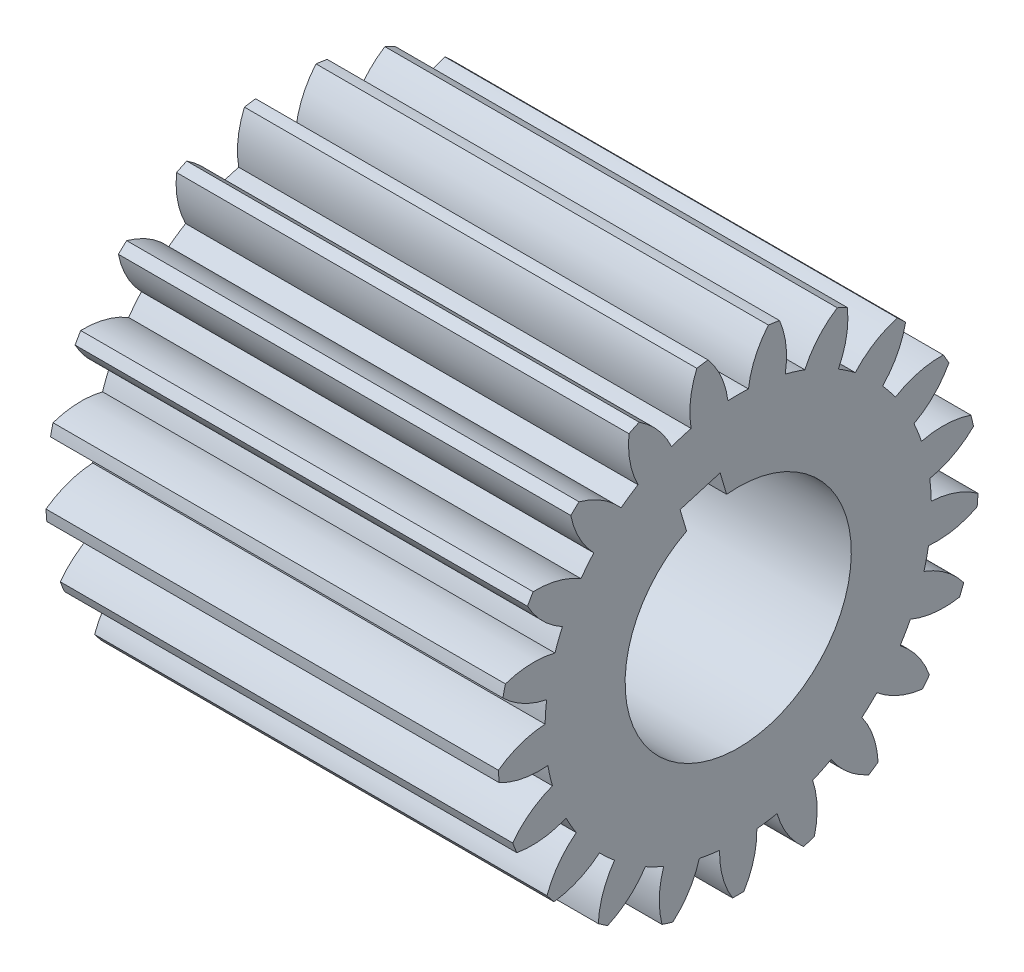
SolidWorks part; units mm, degrees
ref_plane "Plane1" through (0, 0, 0) normal (0, 0, 1) x (1, 0, 0)
ref_plane "Plane2" through (0, 0, 0) normal (0, 1, 0) x (1, 0, 0)
ref_plane "Plane3" through (0, 0, 0) normal (1, 0, 0) x (0, 0, -1)
other "Configuration Table"
sketch "HoldingSke" plane through (0, 0, 0) normal (0, 1, 0) x (1, 0, 0)
  line L0 (0, 0) -> (0.1556, -0.0597)
  line L1 (-15, 0) -> (100, 0) construction
  line L2 (0, 0) -> (-2.1039, 2.3779)
  line L3 (0, 0) -> (-11.863, 4.5341)
  line L4 (0, 0) -> (8.0624, 3.0949)
  line L5 (0, 0) -> (-46.8476, -17.4728)
  line L6 (0, 0) -> (-107.7652, -72.7095)
  line L7 (-2.1039, 2.3779) -> (25.8785, 129.3306)
  line L8 (-76.2, 54.61) -> (-71.3, 54.61)
  line L9 (-71.009, 38.7566) -> (-53.1078, 45.2721)
  line L10 (-76.2, 71.12) -> (104.1128, 71.12)
  line L11 (0, 0) -> (-130, 0)
  line L12 (-76.2, 101.6) -> (-75.993, 101.6)
  line L13 (24.9733, 27.94) -> (52.9518, 28.4284)
  line L14 (24.9733, 27.94) -> (24.9743, 27.94)
  line L15 (24.9733, 27.94) -> (100.4006, 29.5858)
  line L16 (-63.627, -6) -> (-12.827, -6)
  circle A0 centre (0, 0) radius 32.5
  circle A1 centre (0, 0) radius 37.5
  circle A2 centre (0, 0) radius 37.5
  circle A3 centre (0, 0) radius 32.5
  dimension "MHD" = 75
  dimension "Hub_dia" = 75
  dimension "Bore" = 65
  dimension "MBD" = 65
  dimension "Num_teeth" = 21
  dimension "Pitch" = 0.1667
  dimension "Overall_len" = 50
  dimension "Show_teeth" = 21
  dimension "Thickness" = 130
  dimension "OAL" = 130.0001
  dimension "T_dim" = 4.9
  dimension "Ap" = 20
  dimension "H" = 19.05
  dimension "Pitch_radius" = 180.3128
  dimension "Width" = 130
  dimension "Backlash" = 0.207
  dimension "Addendum_fac" = 1
  dimension "Dedendum_fac" = 1.25
  dimension "Clearance_fac" = 0.25
  dimension "Dedendum_add" = 0.001
  dimension "Module" = 6
sketch "BasProSke" plane through (0, 0, 0) normal (0, 1, 0) x (1, 0, 0)
  line L0 (-10, 0) -> (60, 0) construction
  line L1 (0, 0) -> (0, 69)
  line L2 (0, 0) -> (130, 0)
  line L3 (130, 0) -> (130, 69)
  line L4 (130, 69) -> (0, 69)
  dimension "Thickness" = 130
  dimension "Diameter" = 138
revolve "Base-Revolve" add sketch "BasProSke" angle 360 about L0
sketch "TooCutSke" plane through (0, 0, 0) normal (1, 0, 0) x (0, 0, -1)
  line L1 (0, 0) -> (0, 107) construction
  line L2 (0, 0) -> (-5.0701, 62.7957) construction
  line L3 (0, 0) -> (-18.7346, 124.2959) construction
  line L4 (-5.0701, 62.7957) -> (-9.3673, 62.148) construction
  arc A0 (2.9399, 55.4211) -> (-2.9399, 55.4211) centre (0, 0) ccw
  arc A1 (8.6963, 68.4754) -> (-8.6963, 68.4754) centre (0, 0) ccw
  circle A2 centre (0, 0) radius 63 construction
  circle A3 centre (0, 0) radius 59.2006 construction
  arc A4 (-2.9399, 55.4211) -> (-8.6963, 68.4754) centre (-27.9327, 52.1965) ccw
  arc A5 (8.6963, 68.4754) -> (2.9399, 55.4211) centre (27.9327, 52.1965) ccw
  dimension "Root_dia" = 110.998
  dimension "Overcut_dia" = 138.0508
  dimension "Pitch_dia" = 126
  dimension "Base_dia" = 118.4013
  dimension "Flank_rad" = 25.2
  dimension "Half_ang" = 8.571
  dimension "Half_CT" = 4.3457
extrude "ToothCut" cut sketch "TooCutSke" along normal through all
fillet "Breaks" [suppressed] radius 0.12
fillet "RootFillets" [suppressed] radius 1.501
pattern_circular "TeethCuts" count 21 every 17.143 about axis through (-10, 0, 0) along (1, 0, 0) of "ToothCut", "RootFillets", "Breaks"
sketch "HubNeaOneSke" plane through (0, 0, 0) normal (-1, 0, 0) x (0, 0, 1)
  circle A0 centre (0, 0) radius 37.5
  dimension "Diameter" = 75
extrude "HubNearOne" [suppressed] add sketch "HubNeaOneSke" along normal blind 38.0001
sketch "HubNeaBotSke" plane through (0, 0, 0) normal (-1, 0, 0) x (0, 0, 1)
  circle A0 centre (0, 0) radius 37.5
  dimension "Diameter" = 75
extrude "HubNearBoth" [suppressed] add sketch "HubNeaBotSke" along normal blind 19
ref_plane "FarPln" through (130, 0, 0) normal (1, 0, 0) x (0, 0, -1)
sketch "HubFarSke" plane through (130, 0, 0) normal (1, 0, 0) x (0, 0, -1)
  circle A0 centre (0, 0) radius 37.5
  dimension "Diameter" = 75
extrude "HubFar" [suppressed] add sketch "HubFarSke" along normal blind 19
sketch "BorSke" plane through (0, 0, 0) normal (1, 0, 0) x (0, 0, -1)
  circle A0 centre (0, 0) radius 32.5
  dimension "Diameter" = 65
extrude "Bore" cut sketch "BorSke" along normal mid plane 260.0001
sketch "KeySke" plane through (0, 0, 0) normal (1, 0, 0) x (0, 0, -1)
  line L0 (-10, 0) -> (-10, 37.4)
  line L1 (-10, 37.4) -> (10, 37.4)
  line L2 (10, 37.4) -> (10, 0)
  line L3 (0, 0) -> (0, 34) construction
  line L4 (-10, 0) -> (10, 0)
  dimension "Offset" = 37.4
  dimension "Width" = 20
extrude "Keyway" [suppressed] cut sketch "KeySke" along normal mid plane 260.0001
pattern_circular "Keyway2" [suppressed] count 2 every 90 about axis through (-10, 0, 0) along (1, 0, 0)
sketch "Sketch1" plane through (0, 0, 0) normal (-1, 0, 0) x (0, 0, 1)
  line L0 (16.6951, 35.2069) -> (5.19, 38.6175) construction
  line L1 (16.6951, 35.2069) -> (5.19, 38.6175)
  line L2 (5.19, 38.6175) -> (1.7794, 27.1124) construction
  line L3 (13.2845, 23.7018) -> (1.7794, 27.1124) construction
  line L4 (16.6951, 35.2069) -> (13.2845, 23.7018) construction
  line L5 (5.19, 38.6175) -> (1.7794, 27.1124)
  line L6 (13.2845, 23.7018) -> (1.7794, 27.1124)
  line L7 (16.6951, 35.2069) -> (13.2845, 23.7018)
  arc A84 (55.0464, 7.0733) -> (67.6125, 13.7679) centre (49.9632, 31.7552) ccw
  arc A85 (67.6125, 13.7679) -> (66.8904, 16.9315) centre (0, 0) ccw
  arc A86 (66.8904, 16.9315) -> (52.6641, 17.511) centre (58.7934, -6.9323) ccw
  arc A87 (52.6641, 17.511) -> (50.516, 22.9842) centre (0, 0) ccw
  arc A88 (50.516, 22.9842) -> (60.5505, 33.0854) centre (38.3834, 45.0714) ccw
  arc A89 (60.5505, 33.0854) -> (58.928, 35.8955) centre (0, 0) ccw
  arc A90 (58.928, 35.8955) -> (45.1629, 32.256) centre (58.2247, 10.7054) ccw
  arc A91 (45.1629, 32.256) -> (41.497, 36.8529) centre (0, 0) ccw
  arc A92 (41.497, 36.8529) -> (48.1083, 49.4631) centre (23.3932, 54.3827) ccw
  arc A93 (48.1083, 49.4631) -> (45.7296, 51.6701) centre (0, 0) ccw
  arc A94 (45.7296, 51.6701) -> (33.6488, 44.135) centre (52.4824, 27.3918) ccw
  arc A95 (33.6488, 44.135) -> (28.7908, 47.4471) centre (0, 0) ccw
  arc A96 (28.7908, 47.4471) -> (31.3915, 61.4457) centre (6.3243, 58.8619) ccw
  arc A97 (31.3915, 61.4457) -> (28.4679, 62.8536) centre (0, 0) ccw
  arc A98 (28.4679, 62.8536) -> (19.1449, 52.0923) centre (42.0769, 41.6443) ccw
  arc A99 (19.1449, 52.0923) -> (13.5264, 53.8254) centre (0, 0) ccw
  arc A100 (13.5264, 53.8254) -> (11.8854, 67.9687) centre (-11.3065, 58.1109) ccw
  arc A101 (11.8854, 67.9687) -> (8.6768, 68.4523) centre (0, 0) ccw
  arc A102 (8.6768, 68.4523) -> (2.9399, 55.4211) centre (27.9327, 52.1965) ccw
  arc A103 (2.9399, 55.4211) -> (-2.9399, 55.4211) centre (0, 0) ccw
  arc A104 (-2.9399, 55.4211) -> (-8.6768, 68.4523) centre (-27.9327, 52.1965) ccw
  arc A105 (-8.6768, 68.4523) -> (-11.8854, 67.9687) centre (0, 0) ccw
  arc A106 (-11.8854, 67.9687) -> (-13.5264, 53.8254) centre (11.3065, 58.1109) ccw
  arc A107 (-13.5264, 53.8254) -> (-19.1449, 52.0923) centre (0, 0) ccw
  arc A108 (-19.1449, 52.0923) -> (-28.4679, 62.8536) centre (-42.0769, 41.6443) ccw
  arc A109 (-28.4679, 62.8536) -> (-31.3915, 61.4457) centre (0, 0) ccw
  arc A110 (-31.3915, 61.4457) -> (-28.7908, 47.4471) centre (-6.3243, 58.8619) ccw
  arc A111 (-28.7908, 47.4471) -> (-33.6488, 44.135) centre (0, 0) ccw
  arc A112 (-33.6488, 44.135) -> (-45.7296, 51.6701) centre (-52.4824, 27.3918) ccw
  arc A113 (-45.7296, 51.6701) -> (-48.1083, 49.4631) centre (0, 0) ccw
  arc A114 (-48.1083, 49.4631) -> (-41.497, 36.8529) centre (-23.3932, 54.3827) ccw
  arc A115 (-41.497, 36.8529) -> (-45.1629, 32.256) centre (0, 0) ccw
  arc A116 (-45.1629, 32.256) -> (-58.928, 35.8955) centre (-58.2247, 10.7054) ccw
  arc A117 (-58.928, 35.8955) -> (-60.5505, 33.0854) centre (0, 0) ccw
  arc A118 (-60.5505, 33.0854) -> (-50.516, 22.9842) centre (-38.3834, 45.0714) ccw
  arc A119 (-50.516, 22.9842) -> (-52.6641, 17.511) centre (0, 0) ccw
  arc A120 (-52.6641, 17.511) -> (-66.8904, 16.9315) centre (-58.7934, -6.9323) ccw
  arc A121 (-66.8904, 16.9315) -> (-67.6125, 13.7679) centre (0, 0) ccw
  arc A122 (-67.6125, 13.7679) -> (-55.0464, 7.0733) centre (-49.9632, 31.7552) ccw
  arc A123 (-55.0464, 7.0733) -> (-55.4858, 1.21) centre (0, 0) ccw
  arc A124 (-55.4858, 1.21) -> (-68.9093, -3.537) centre (-54.138, -23.9539) ccw
  arc A125 (-68.9093, -3.537) -> (-68.6668, -6.7729) centre (0, 0) ccw
  arc A126 (-68.6668, -6.7729) -> (-54.6857, -9.4662) centre (-57.1035, 15.6175) ccw
  arc A127 (-54.6857, -9.4662) -> (-53.3774, -15.1985) centre (0, 0) ccw
  arc A128 (-53.3774, -15.1985) -> (-64.8053, -23.6913) centre (-44.6723, -38.8472) ccw
  arc A129 (-64.8053, -23.6913) -> (-63.6198, -26.7118) centre (0, 0) ccw
  arc A130 (-63.6198, -26.7118) -> (-49.466, -25.1646) centre (-59.1699, -1.9078) ccw
  arc A131 (-49.466, -25.1646) -> (-46.5261, -30.2565) centre (0, 0) ccw
  arc A132 (-46.5261, -30.2565) -> (-54.943, -41.7404) centre (-31.2372, -50.2887) ccw
  arc A133 (-54.943, -41.7404) -> (-52.9199, -44.2774) centre (0, 0) ccw
  arc A134 (-52.9199, -44.2774) -> (-39.851, -38.6269) centre (-55.9788, -19.2637) ccw
  arc A135 (-39.851, -38.6269) -> (-35.5408, -42.6261) centre (0, 0) ccw
  arc A136 (-35.5408, -42.6261) -> (-40.1989, -56.0808) centre (-15.0266, -57.2618) ccw
  arc A137 (-40.1989, -56.0808) -> (-37.5178, -57.9087) centre (0, 0) ccw
  arc A138 (-37.5178, -57.9087) -> (-26.695, -48.6571) centre (-47.8137, -34.9079) ccw
  arc A139 (-26.695, -48.6571) -> (-21.3976, -51.2082) centre (0, 0) ccw
  arc A140 (-21.3976, -51.2082) -> (-21.8828, -65.4381) centre (2.5193, -59.147) ccw
  arc A141 (-21.8828, -65.4381) -> (-18.7821, -66.3945) centre (0, 0) ccw
  arc A142 (-18.7821, -66.3945) -> (-11.1671, -54.3639) centre (-35.4002, -47.4504) ccw
  arc A143 (-11.1671, -54.3639) -> (-5.3531, -55.2402) centre (0, 0) ccw
  arc A144 (-5.3531, -55.2402) -> (-1.6224, -68.9809) centre (19.8412, -55.7767) ccw
  arc A145 (-1.6224, -68.9809) -> (1.6224, -68.9809) centre (0, 0) ccw
  arc A146 (1.6224, -68.9809) -> (5.3531, -55.2402) centre (-19.8412, -55.7767) ccw
  arc A147 (5.3531, -55.2402) -> (11.1671, -54.3639) centre (0, 0) ccw
  arc A148 (11.1671, -54.3639) -> (18.7821, -66.3945) centre (35.4002, -47.4504) ccw
  arc A149 (18.7821, -66.3945) -> (21.8828, -65.4381) centre (0, 0) ccw
  arc A150 (21.8828, -65.4381) -> (21.3976, -51.2082) centre (-2.5193, -59.147) ccw
  arc A151 (21.3976, -51.2082) -> (26.695, -48.6571) centre (0, 0) ccw
  arc A152 (26.695, -48.6571) -> (37.5178, -57.9087) centre (47.8137, -34.9079) ccw
  arc A153 (37.5178, -57.9087) -> (40.1989, -56.0808) centre (0, 0) ccw
  arc A154 (40.1989, -56.0808) -> (35.5408, -42.6261) centre (15.0266, -57.2618) ccw
  arc A155 (35.5408, -42.6261) -> (39.851, -38.6269) centre (0, 0) ccw
  arc A156 (39.851, -38.6269) -> (52.9199, -44.2774) centre (55.9788, -19.2637) ccw
  arc A157 (52.9199, -44.2774) -> (54.943, -41.7404) centre (0, 0) ccw
  arc A158 (54.943, -41.7404) -> (46.5261, -30.2565) centre (31.2372, -50.2887) ccw
  arc A159 (46.5261, -30.2565) -> (49.466, -25.1646) centre (0, 0) ccw
  arc A160 (49.466, -25.1646) -> (63.6198, -26.7118) centre (59.1699, -1.9078) ccw
  arc A161 (63.6198, -26.7118) -> (64.8053, -23.6913) centre (0, 0) ccw
  arc A162 (64.8053, -23.6913) -> (53.3774, -15.1985) centre (44.6723, -38.8472) ccw
  arc A163 (53.3774, -15.1985) -> (54.6857, -9.4662) centre (0, 0) ccw
  arc A164 (54.6857, -9.4662) -> (68.6668, -6.7729) centre (57.1035, 15.6175) ccw
  arc A165 (68.6668, -6.7729) -> (68.9093, -3.537) centre (0, 0) ccw
  arc A166 (68.9093, -3.537) -> (55.4858, 1.21) centre (54.138, -23.9539) ccw
  arc A167 (55.4858, 1.21) -> (55.0464, 7.0733) centre (0, 0) ccw
  arc A168 (55.0464, 7.0733) -> (67.6125, 13.7679) centre (49.9632, 31.7552) ccw
  arc A169 (67.6125, 13.7679) -> (66.8904, 16.9315) centre (0, 0) ccw
  arc A170 (66.8904, 16.9315) -> (52.6641, 17.511) centre (58.7934, -6.9323) ccw
  arc A171 (52.6641, 17.511) -> (50.516, 22.9842) centre (0, 0) ccw
  arc A172 (50.516, 22.9842) -> (60.5505, 33.0854) centre (38.3834, 45.0714) ccw
  arc A173 (60.5505, 33.0854) -> (58.928, 35.8955) centre (0, 0) ccw
  arc A174 (58.928, 35.8955) -> (45.1629, 32.256) centre (58.2247, 10.7054) ccw
  arc A175 (45.1629, 32.256) -> (41.497, 36.8529) centre (0, 0) ccw
  arc A176 (41.497, 36.8529) -> (48.1083, 49.4631) centre (23.3932, 54.3827) ccw
  arc A177 (48.1083, 49.4631) -> (45.7296, 51.6701) centre (0, 0) ccw
  arc A178 (45.7296, 51.6701) -> (33.6488, 44.135) centre (52.4824, 27.3918) ccw
  arc A179 (33.6488, 44.135) -> (28.7908, 47.4471) centre (0, 0) ccw
  arc A180 (28.7908, 47.4471) -> (31.3915, 61.4457) centre (6.3243, 58.8619) ccw
  arc A181 (31.3915, 61.4457) -> (28.4679, 62.8536) centre (0, 0) ccw
  arc A182 (28.4679, 62.8536) -> (19.1449, 52.0923) centre (42.0769, 41.6443) ccw
  arc A183 (19.1449, 52.0923) -> (13.5264, 53.8254) centre (0, 0) ccw
  arc A184 (13.5264, 53.8254) -> (11.8854, 67.9687) centre (-11.3065, 58.1109) ccw
  arc A185 (11.8854, 67.9687) -> (8.6768, 68.4523) centre (0, 0) ccw
  arc A186 (8.6768, 68.4523) -> (2.9399, 55.4211) centre (27.9327, 52.1965) ccw
  arc A187 (2.9399, 55.4211) -> (-2.9399, 55.4211) centre (0, 0) ccw
  arc A188 (-2.9399, 55.4211) -> (-8.6768, 68.4523) centre (-27.9327, 52.1965) ccw
  arc A189 (-8.6768, 68.4523) -> (-11.8854, 67.9687) centre (0, 0) ccw
  arc A190 (-11.8854, 67.9687) -> (-13.5264, 53.8254) centre (11.3065, 58.1109) ccw
  arc A191 (-13.5264, 53.8254) -> (-19.1449, 52.0923) centre (0, 0) ccw
  arc A192 (-19.1449, 52.0923) -> (-28.4679, 62.8536) centre (-42.0769, 41.6443) ccw
  arc A193 (-28.4679, 62.8536) -> (-31.3915, 61.4457) centre (0, 0) ccw
  arc A194 (-31.3915, 61.4457) -> (-28.7908, 47.4471) centre (-6.3243, 58.8619) ccw
  arc A195 (-28.7908, 47.4471) -> (-33.6488, 44.135) centre (0, 0) ccw
  arc A196 (-33.6488, 44.135) -> (-45.7296, 51.6701) centre (-52.4824, 27.3918) ccw
  arc A197 (-45.7296, 51.6701) -> (-48.1083, 49.4631) centre (0, 0) ccw
  arc A198 (-48.1083, 49.4631) -> (-41.497, 36.8529) centre (-23.3932, 54.3827) ccw
  arc A199 (-41.497, 36.8529) -> (-45.1629, 32.256) centre (0, 0) ccw
  arc A200 (-45.1629, 32.256) -> (-58.928, 35.8955) centre (-58.2247, 10.7054) ccw
  arc A201 (-58.928, 35.8955) -> (-60.5505, 33.0854) centre (0, 0) ccw
  arc A202 (-60.5505, 33.0854) -> (-50.516, 22.9842) centre (-38.3834, 45.0714) ccw
  arc A203 (-50.516, 22.9842) -> (-52.6641, 17.511) centre (0, 0) ccw
  arc A204 (-52.6641, 17.511) -> (-66.8904, 16.9315) centre (-58.7934, -6.9323) ccw
  arc A205 (-66.8904, 16.9315) -> (-67.6125, 13.7679) centre (0, 0) ccw
  arc A206 (-67.6125, 13.7679) -> (-55.0464, 7.0733) centre (-49.9632, 31.7552) ccw
  arc A207 (-55.0464, 7.0733) -> (-55.4858, 1.21) centre (0, 0) ccw
  arc A208 (-55.4858, 1.21) -> (-68.9093, -3.537) centre (-54.138, -23.9539) ccw
  arc A209 (-68.9093, -3.537) -> (-68.6668, -6.7729) centre (0, 0) ccw
  arc A210 (-68.6668, -6.7729) -> (-54.6857, -9.4662) centre (-57.1035, 15.6175) ccw
  arc A211 (-54.6857, -9.4662) -> (-53.3774, -15.1985) centre (0, 0) ccw
  arc A212 (-53.3774, -15.1985) -> (-64.8053, -23.6913) centre (-44.6723, -38.8472) ccw
  arc A213 (-64.8053, -23.6913) -> (-63.6198, -26.7118) centre (0, 0) ccw
  arc A214 (-63.6198, -26.7118) -> (-49.466, -25.1646) centre (-59.1699, -1.9078) ccw
  arc A215 (-49.466, -25.1646) -> (-46.5261, -30.2565) centre (0, 0) ccw
  arc A216 (-46.5261, -30.2565) -> (-54.943, -41.7404) centre (-31.2372, -50.2887) ccw
  arc A217 (-54.943, -41.7404) -> (-52.9199, -44.2774) centre (0, 0) ccw
  arc A218 (-52.9199, -44.2774) -> (-39.851, -38.6269) centre (-55.9788, -19.2637) ccw
  arc A219 (-39.851, -38.6269) -> (-35.5408, -42.6261) centre (0, 0) ccw
  arc A220 (-35.5408, -42.6261) -> (-40.1989, -56.0808) centre (-15.0266, -57.2618) ccw
  arc A221 (-40.1989, -56.0808) -> (-37.5178, -57.9087) centre (0, 0) ccw
  arc A222 (-37.5178, -57.9087) -> (-26.695, -48.6571) centre (-47.8137, -34.9079) ccw
  arc A223 (-26.695, -48.6571) -> (-21.3976, -51.2082) centre (0, 0) ccw
  arc A224 (-21.3976, -51.2082) -> (-21.8828, -65.4381) centre (2.5193, -59.147) ccw
  arc A225 (-21.8828, -65.4381) -> (-18.7821, -66.3945) centre (0, 0) ccw
  arc A226 (-18.7821, -66.3945) -> (-11.1671, -54.3639) centre (-35.4002, -47.4504) ccw
  arc A227 (-11.1671, -54.3639) -> (-5.3531, -55.2402) centre (0, 0) ccw
  arc A228 (-5.3531, -55.2402) -> (-1.6224, -68.9809) centre (19.8412, -55.7767) ccw
  arc A229 (-1.6224, -68.9809) -> (1.6224, -68.9809) centre (0, 0) ccw
  arc A230 (1.6224, -68.9809) -> (5.3531, -55.2402) centre (-19.8412, -55.7767) ccw
  arc A231 (5.3531, -55.2402) -> (11.1671, -54.3639) centre (0, 0) ccw
  arc A232 (11.1671, -54.3639) -> (18.7821, -66.3945) centre (35.4002, -47.4504) ccw
  arc A233 (18.7821, -66.3945) -> (21.8828, -65.4381) centre (0, 0) ccw
  arc A234 (21.8828, -65.4381) -> (21.3976, -51.2082) centre (-2.5193, -59.147) ccw
  arc A235 (21.3976, -51.2082) -> (26.695, -48.6571) centre (0, 0) ccw
  arc A236 (26.695, -48.6571) -> (37.5178, -57.9087) centre (47.8137, -34.9079) ccw
  arc A237 (37.5178, -57.9087) -> (40.1989, -56.0808) centre (0, 0) ccw
  arc A238 (40.1989, -56.0808) -> (35.5408, -42.6261) centre (15.0266, -57.2618) ccw
  arc A239 (35.5408, -42.6261) -> (39.851, -38.6269) centre (0, 0) ccw
  arc A240 (39.851, -38.6269) -> (52.9199, -44.2774) centre (55.9788, -19.2637) ccw
  arc A241 (52.9199, -44.2774) -> (54.943, -41.7404) centre (0, 0) ccw
  arc A242 (54.943, -41.7404) -> (46.5261, -30.2565) centre (31.2372, -50.2887) ccw
  arc A243 (46.5261, -30.2565) -> (49.466, -25.1646) centre (0, 0) ccw
  arc A244 (49.466, -25.1646) -> (63.6198, -26.7118) centre (59.1699, -1.9078) ccw
  arc A245 (63.6198, -26.7118) -> (64.8053, -23.6913) centre (0, 0) ccw
  arc A246 (64.8053, -23.6913) -> (53.3774, -15.1985) centre (44.6723, -38.8472) ccw
  arc A247 (53.3774, -15.1985) -> (54.6857, -9.4662) centre (0, 0) ccw
  arc A248 (54.6857, -9.4662) -> (68.6668, -6.7729) centre (57.1035, 15.6175) ccw
  arc A249 (68.6668, -6.7729) -> (68.9093, -3.537) centre (0, 0) ccw
  arc A250 (68.9093, -3.537) -> (55.4858, 1.21) centre (54.138, -23.9539) ccw
  arc A251 (55.4858, 1.21) -> (55.0464, 7.0733) centre (0, 0) ccw
  dimension "D1" = 0
extrude "Cut-Extrude1" cut sketch "Sketch1" against normal through all contours L7 L1 L5 L6
equation "' \"Module@HoldingSke\" = 6.35"
equation "' \"Num_teeth@HoldingSke\" = 12"
equation "' \"Ap@HoldingSke\" =  20"
equation "' \"Ap@HoldingSke\" = 20"
equation "' \"Width@HoldingSke\" = 0.5 * 25.4"
equation "' \"Hub_dia@HoldingSke\"= 1 * 25.4"
equation "' \"Hub_dia@HoldingSke\" = 1 * 25.4"
equation "' \"Overall_len@HoldingSke\" = 1.0 * 25.4"
equation "' \"Bore@HoldingSke\" = 0.75 * 25.4"
equation "' \"T_dim@HoldingSke\" = 0.1 * 25.4"
equation "' \"Width@KeySke\" = 0.25 * 25.4"
equation "' \"Show_teeth@HoldingSke\" = 13"
equation "' \"Backlash@HoldingSke\" = 0.009 * 25.4"
equation "' \"Addendum_fac@HoldingSke\" = 1.0"
equation "' \"Dedendum_fac@HoldingSke\" = 1.25"
equation "' \"Dedendum_add@HoldingSke\" = 0.00005 * 25.4"
equation "' \"Clearance_fac@HoldingSke\" = 0.25"
equation "\"Pitch@HoldingSke\" = 1 / \"Module@HoldingSke\""
equation "\"Overcut_dia@TooCutSke\" = (\"Num_teeth@HoldingSke\" + 2 * \"Addendum_fac@HoldingSke\") / \"Pitch@HoldingSke\" + 0.002 * 25.4"
equation "\"Pitch_dia@TooCutSke\" = \"Num_teeth@HoldingSke\" / \"Pitch@HoldingSke\""
equation "\"Base_dia@TooCutSke\" = \"Num_teeth@HoldingSke\" / \"Pitch@HoldingSke\" * cos((\"Ap@HoldingSke\"  * 3.14159265 / 180))"
equation "\"Root_dia@TooCutSke\" = (\"Num_teeth@HoldingSke\" + 2) / \"Pitch@HoldingSke\" - 2 * (\"Addendum_fac@HoldingSke\" + \"Dedendum_fac@HoldingSke\") / \"Pitch@HoldingSke\" - \"Dedendum_add@HoldingSke\" * 2"
equation "\"Half_ang@TooCutSke\" = 180 / \"Num_teeth@HoldingSke\""
equation "\"Half_CT@TooCutSke\" = \"Num_teeth@HoldingSke\" / \"Pitch@HoldingSke\" * sin((3.14159265 / 2 / \"Num_teeth@HoldingSke\")) / 2 - 7 * \"Backlash@HoldingSke\" / 4"
equation "\"Flank_rad@TooCutSke\" = \"Num_teeth@HoldingSke\" / \"Pitch@HoldingSke\" / 5"
equation "\"Radius@RootFillets\" = \"Clearance_fac@HoldingSke\" / \"Pitch@HoldingSke\" + \"Dedendum_add@HoldingSke\""
equation "\"Break_rad@Breaks\" = 0.02 / \"Pitch@HoldingSke\""
equation "\"Thickness@HoldingSke\" = \"Width@HoldingSke\""
equation "\"OAL@HoldingSke\" = \"Thickness@HoldingSke\""
equation "\"MHD@HoldingSke\" = (\"Num_teeth@HoldingSke\" + 2) / \"Pitch@HoldingSke\" - 2 * (\"Addendum_fac@HoldingSke\" + \"Dedendum_fac@HoldingSke\")  / \"Pitch@HoldingSke\" - \"Dedendum_add@HoldingSke\" * 2"
equation "\"MBD@HoldingSke\" = (\"Num_teeth@HoldingSke\" + 2) / \"Pitch@HoldingSke\" - 2 * (\"Addendum_fac@HoldingSke\" + \"Dedendum_fac@HoldingSke\")  / \"Pitch@HoldingSke\" - \"Dedendum_add@HoldingSke\" * 2 - 0.002 * 25.4"
equation "\"MHD@HoldingSke\" = ((sgn( \"MHD@HoldingSke\" - \"Hub_dia@HoldingSke\" )-1)*( \"MHD@HoldingSke\" - \"Hub_dia@HoldingSke\" ))/-2+ \"Hub_dia@HoldingSke\""
equation "\"MBD@HoldingSke\" = ((sgn( \"MBD@HoldingSke\" - \"Bore@HoldingSke\" )-1)*( \"MBD@HoldingSke\" - \"Bore@HoldingSke\" ))/-2+ \"Bore@HoldingSke\""
equation "\"OAL@HoldingSke\" = ((sgn( \"OAL@HoldingSke\" - \"Overall_len@HoldingSke\" )+1)*( \"OAL@HoldingSke\" - \"Overall_len@HoldingSke\" ))/2 + \"Overall_len@HoldingSke\" + 0.000002 * 25.4"
equation "\"Num_teeth@TeethCuts\" = int( \"Show_teeth@HoldingSke\" ) + 1"
equation "\"Num_teeth@TeethCuts\" = ((sgn( \"Num_teeth@TeethCuts\" - \"Num_teeth@HoldingSke\" )-1)*( \"Num_teeth@TeethCuts\" - \"Num_teeth@HoldingSke\" ))/-2+ \"Num_teeth@HoldingSke\""
equation "\"Num_teeth@TeethCuts\" = ((sgn( \"Num_teeth@TeethCuts\" - 2.0)+1)*( \"Num_teeth@TeethCuts\" - 2.0))/2 +2.0"
equation "\"Angle@TeethCuts\" = 360.0 / \"Num_teeth@HoldingSke\""
equation "\"Diameter@BasProSke\" = (\"Num_teeth@HoldingSke\" + 2 * \"Addendum_fac@HoldingSke\") / \"Pitch@HoldingSke\""
equation "\"Thickness@BasProSke\"  = \"Thickness@HoldingSke\""
equation "' \"Fillet_rad@BasProSke\" =  \"Thickness@HoldingSke\" * 0.05"
equation "' \"Fillet_rad@BasProSke\" = \"Thickness@HoldingSke\" * 0.05"
equation "\"MHD@HoldingSke\" = ((sgn( \"MHD@HoldingSke\" - \"Root_dia@TooCutSke\" )-1)*( \"MHD@HoldingSke\" - \"Root_dia@TooCutSke\" ))/-2+ \"Root_dia@TooCutSke\""
equation "\"Diameter@HubNeaOneSke\" = \"MHD@HoldingSke\""
equation "\"Length@HubNearOne\" = \"OAL@HoldingSke\" - \"Thickness@BasProSke\""
equation "\"Diameter@HubNeaBotSke\" = \"MHD@HoldingSke\""
equation "\"Length@HubNearBoth\" = ( \"OAL@HoldingSke\" - \"Thickness@BasProSke\" ) / 2.0"
equation "\"Thickness@FarPln\" = \"Thickness@BasProSke\""
equation "\"Diameter@HubFarSke\" = \"MHD@HoldingSke\""
equation "\"Length@HubFar\" = ( \"OAL@HoldingSke\" - \"Thickness@BasProSke\" ) / 2.0"
equation "\"Diameter@BorSke\" = \"MBD@HoldingSke\""
equation "\"D1@Bore\" = \"OAL@HoldingSke\" * 2.0"
equation "\"D1@Keyway\" = \"OAL@HoldingSke\" * 2.0"
equation "\"Offset@KeySke\" = \"T_dim@HoldingSke\" + \"MBD@HoldingSke\" / 2.0"
